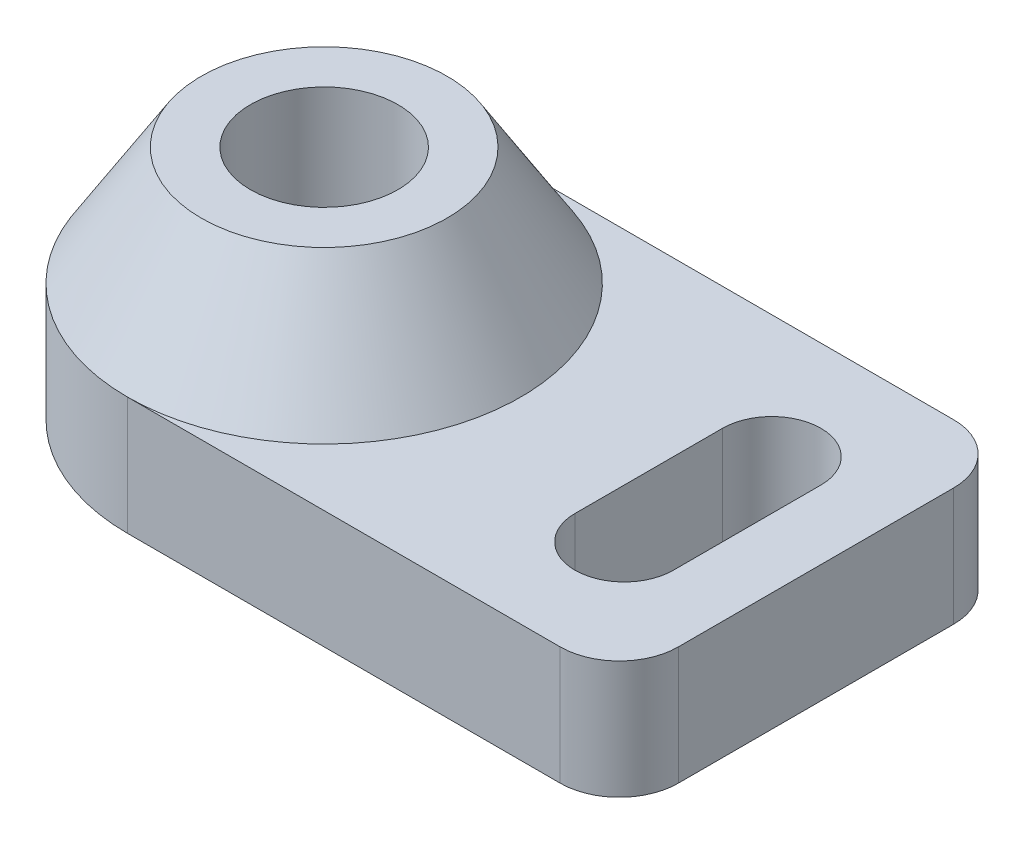
SolidWorks part; units mm, degrees
ref_plane "Ön Düzlem" through (0, 0, 0) normal (0, 0, 1) x (1, 0, 0)
ref_plane "Üst Düzlem" through (0, 0, 0) normal (0, 1, 0) x (1, 0, 0)
ref_plane "Sağ Düzlem" through (0, 0, 0) normal (1, 0, 0) x (0, 0, -1)
sketch "Çizim1" plane through (0, 0, 0) normal (0, 1, 0) x (1, 0, 0)
  line L1 (0, 0) -> (-25, 0)
  line L2 (0, 0) -> (0, 20)
  line L3 (0, 20) -> (-25, 20)
  line L4 (-25, 0) -> (-25, 20)
  circle A0 centre (-25, 10) radius 10
  dimension "D3" = 20
  dimension "D1" = 25
  dimension "D2" = 20
extrude "Yükseklik-Ekstrüzyon1" add sketch "Çizim1" along normal blind 6 contours L4 A0 | A0 L1 L2 L3 | L4 A0
sketch "Çizim2" plane through (0, 6, 0) normal (0, 1, 0) x (1, 0, 0)
  circle A0 centre (-25, 10) radius 10
  circle A1 centre (-25, 10) radius 6.25
  circle A2 centre (-25, 10) radius 3.75
  dimension "D1" = 20
  dimension "D2" = 12.5
  dimension "D3" = 7.5
extrude "Yükseklik-Ekstrüzyon2" add sketch "Çizim2" along normal blind 6 contours A1 A2
sketch "Çizim3" plane through (0, 6, 0) normal (0, 1, 0) x (1, 0, 0)
  circle A0 centre (-25, 10) radius 10
  point P3 (0, 0)
  dimension "D1" = 20
sketch "Çizim4" plane through (0, 6, 0) normal (0, 1, 0) x (1, 0, 0)
  line L0 (-6, 13.75) -> (-6, 6.25) construction
  line L1 (-3.5, 13.75) -> (-3.5, 6.25)
  line L2 (-8.5, 13.75) -> (-8.5, 6.25)
  line L3 (0, 0) -> (0, 20) construction
  line L4 (0, 0) -> (-25, 0) construction
  arc A0 (-3.5, 13.75) -> (-8.5, 13.75) centre (-6, 13.75) ccw
  arc A1 (-8.5, 6.25) -> (-3.5, 6.25) centre (-6, 6.25) ccw
  point P2 (-6, 10)
  dimension "D1" = 5
  dimension "D2" = 6
  dimension "D3" = 7.5
  dimension "D4" = 6.25
extrude "Kes-Ekstrüzyon1" cut sketch "Çizim4" against normal blind 6
sketch "Çizim5" plane through (0, 6, 0) normal (0, 1, 0) x (1, 0, 0)
  circle A1 centre (-25, 10) radius 3.75
  dimension "D1" = 7.5
extrude "Kes-Ekstrüzyon2" cut sketch "Çizim5" against normal blind 6
fillet "Radyus1" radius 3 1 edges at (0, 3, 0)
fillet "Radyus2" radius 3 1 edges at (0, 3, -20)
ref_plane "Düzlem1" through (-25, 0, 0) normal (1, 0, 0) x (0, 0, -1)
sketch "Çizim6" plane through (-25, 0, 0) normal (1, 0, 0) x (0, 0, -1)
  line L0 (3.75, 12) -> (0, 6)
  line L1 (0, 6) -> (3.75, 6)
  line L2 (3.75, 12) -> (3.75, 6)
  line L3 (10, 12) -> (10, 0) construction
  line L4 (16.25, 12) -> (3.75, 12) construction
  line L5 (3, 0) -> (17, 0) construction
revolve "Döndür1" add sketch "Çizim6" angle 360 about L3
